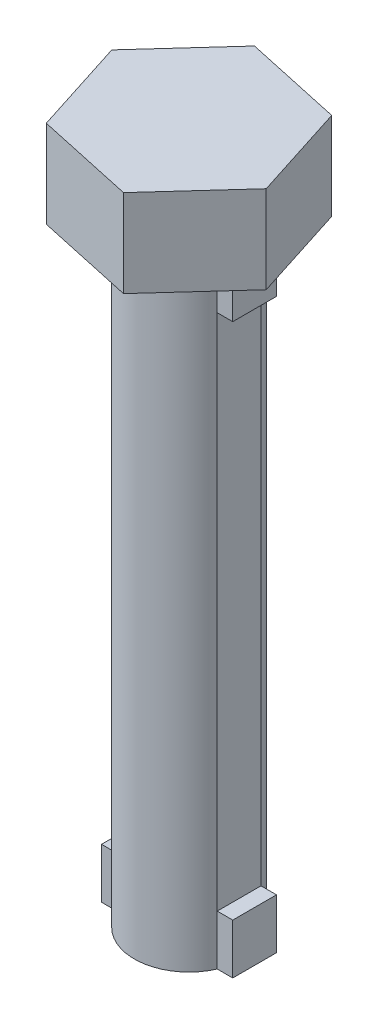
SolidWorks part; units mm, degrees
ref_plane "Front Plane" through (0, 0, 0) normal (0, 0, 1) x (1, 0, 0)
ref_plane "Top Plane" through (0, 0, 0) normal (0, 1, 0) x (1, 0, 0)
ref_plane "Right Plane" through (0, 0, 0) normal (1, 0, 0) x (0, 0, -1)
sketch "Sketch1" plane through (0, 0, 0) normal (0, 1, 0) x (1, 0, 0)
  line L0 (-1.1456, 0.5) -> (-1.5, 0.5)
  line L1 (1.5, 0.5) -> (1.1456, 0.5)
  line L2 (1.5, 0.5) -> (1.5, -0.5)
  line L3 (1.5, -0.5) -> (1.1456, -0.5)
  line L4 (-1.5, 0.5) -> (-1.5, -0.5)
  line L5 (1.5, 0.5) -> (-1.5, -0.5) construction
  line L6 (1.5, -0.5) -> (-1.5, 0.5) construction
  line L7 (-1.1456, -0.5) -> (-1.5, -0.5)
  arc A0 (-1.1456, -0.5) -> (1.1456, -0.5) centre (0, 0) ccw
  arc A1 (1.1456, 0.5) -> (-1.1456, 0.5) centre (0, 0) ccw
  dimension "D1" = 2.5
  dimension "D2" = 1
  dimension "D3" = 3
extrude "Boss-Extrude1" add sketch "Sketch1" along normal blind 14
sketch "Sketch2" plane through (0, 14, 0) normal (0, 1, 0) x (1, 0, 0)
  line L1 (-1.5538, -1.7085) -> (0.7028, -2.1999)
  line L2 (0.7028, -2.1999) -> (2.2565, -0.4913)
  line L3 (2.2565, -0.4913) -> (1.5538, 1.7085)
  line L4 (1.5538, 1.7085) -> (-0.7028, 2.1999)
  line L5 (-0.7028, 2.1999) -> (-2.2565, 0.4913)
  line L6 (-2.2565, 0.4913) -> (-1.5538, -1.7085)
  circle A0 centre (0, 0) radius 2 construction
  dimension "D1" = 4
extrude "Boss-Extrude2" add sketch "Sketch2" along normal blind 2
sketch "Sketch3" plane through (0, 0, 0) normal (0, 0, 1) x (1, 0, 0)
  line L1 (1.5, 0) -> (1.5, 14) construction
  line L3 (1.1456, 14) -> (1.1456, 0) construction
  line L5 (-1.1456, 0) -> (-1.1456, 14) construction
  line L7 (-1.5, 14) -> (-1.5, 0) construction
  line L9 (1.5, 1.147) -> (1.5, 12.9939)
  line L11 (1.1456, 12.9939) -> (1.1456, 1.147)
  line L13 (-1.1456, 1.147) -> (-1.1456, 12.9939)
  line L15 (-1.5, 12.9939) -> (-1.5, 1.147)
  line L16 (-1.5, 12.9939) -> (-1.1456, 12.9939)
  line L17 (-1.5, 1.147) -> (-1.1456, 1.147)
  line L18 (0, 0) -> (0, 2.5814) construction
  line L19 (1.5, 1.147) -> (1.1456, 1.147)
  line L20 (1.5, 12.9939) -> (1.1456, 12.9939)
extrude "Cut-Extrude1" cut sketch "Sketch3" against normal through all both and the other way through all
